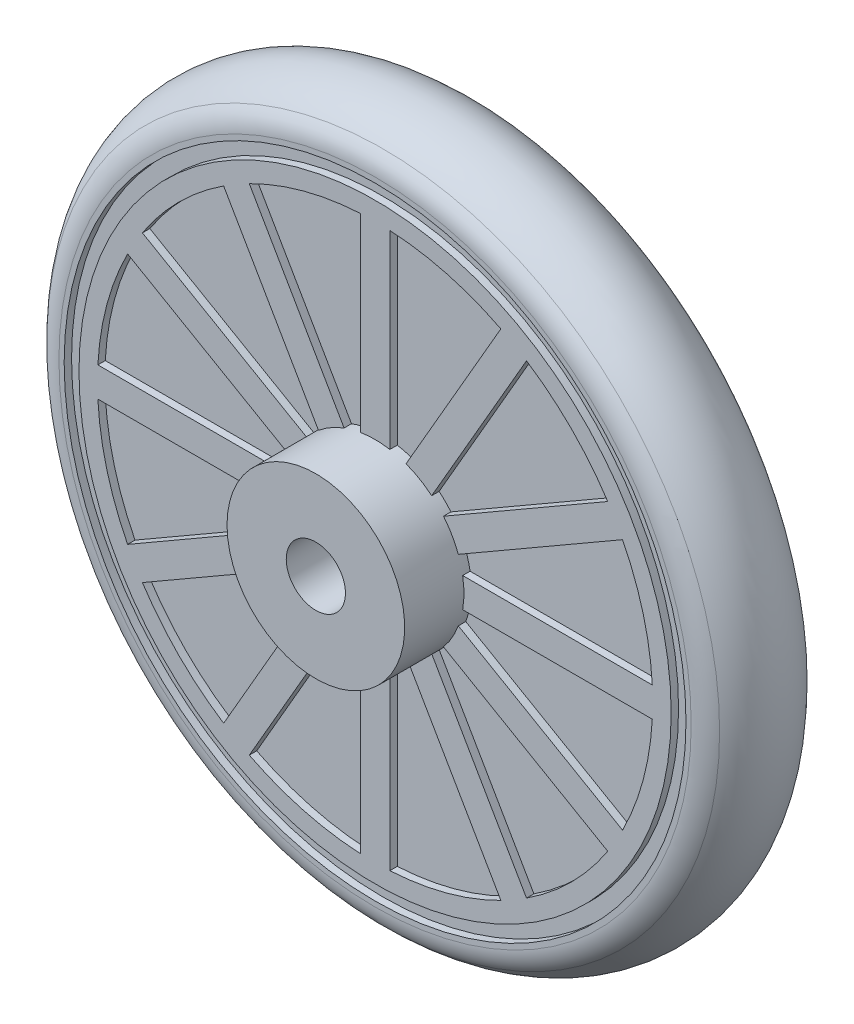
SolidWorks part; units mm, degrees
material "PA Type 6"
ref_plane "Front Plane" through (0, 0, 0) normal (0, 0, 1) x (1, 0, 0)
ref_plane "Top Plane" through (0, 0, 0) normal (0, 1, 0) x (1, 0, 0)
ref_plane "Right Plane" through (0, 0, 0) normal (1, 0, 0) x (0, 0, -1)
sketch "Sketch1" plane through (0, 0, 0) normal (0, 1, 0) x (1, 0, 0)
  line L0 (0, 79.6643) -> (0, 0) construction
  line L1 (0, 0) -> (98.9379, 0) construction
  line L2 (2, 0) -> (2, 7.5)
  line L3 (2, 7.5) -> (6, 7.5)
  line L4 (6, 7.5) -> (6, 3.5)
  line L5 (6, 3.5) -> (22, 3.5)
  line L6 (2, 0) -> (24, 0)
  arc A0 (22, 3.5) -> (24, 0) centre (19.9375, 0) cw
  dimension "D1" = 4
  dimension "D2" = 12
  dimension "D3" = 15
  dimension "D4" = 7
  dimension "D5" = 48
  dimension "D6" = 44
revolve "Revolve1" add sketch "Sketch1" angle 360 about L0
sketch "Sketch2" plane through (0, 0, -3.5) normal (0, 0, -1) x (-1, 0, 0)
  circle A0 centre (0, 0) radius 20
  circle A1 centre (0, 0) radius 21
  dimension "D1" = 40
  dimension "D2" = 42
extrude "Cut-Extrude1" cut sketch "Sketch2" against normal blind 0.5
fillet "Fillet1" radius 2 1 edges at (-22, 0, -3.5)
sketch "Sketch3" plane through (0, 0, -3.5) normal (0, 0, -1) x (-1, 0, 0)
  line L0 (0, 28.5204) -> (0, 0) construction
  line L1 (0, 0) -> (15.5992, 27.0187) construction
  line L2 (1, 18.7233) -> (1, 5.9161)
  line L3 (2.092, 5.6235) -> (8.4956, 16.7149)
  line L4 (1, 3.7321) -> (14.7332, 27.5187) construction
  line L5 (1, 28.5204) -> (1, 3.7321) construction
  arc A0 (8.4956, 16.7149) -> (1, 18.7233) centre (0, 0) ccw
  circle A1 centre (0, 0) radius 6 construction
  arc A2 (2.092, 5.6235) -> (1, 5.9161) centre (0, 0) ccw
  dimension "D1" = 37.5
  dimension "D2" = 30
  dimension "D3" = 1
extrude "Cut-Extrude2" cut sketch "Sketch3" against normal blind 0.5
pattern_circular "CirPattern1" count 12 over 360 about axis through (0, 0, 0) along (0, 0, 1) of "Cut-Extrude2"
mirror "Mirror1" about plane through (2, 0, 0) normal (0, 0, -1) of bodies 104
